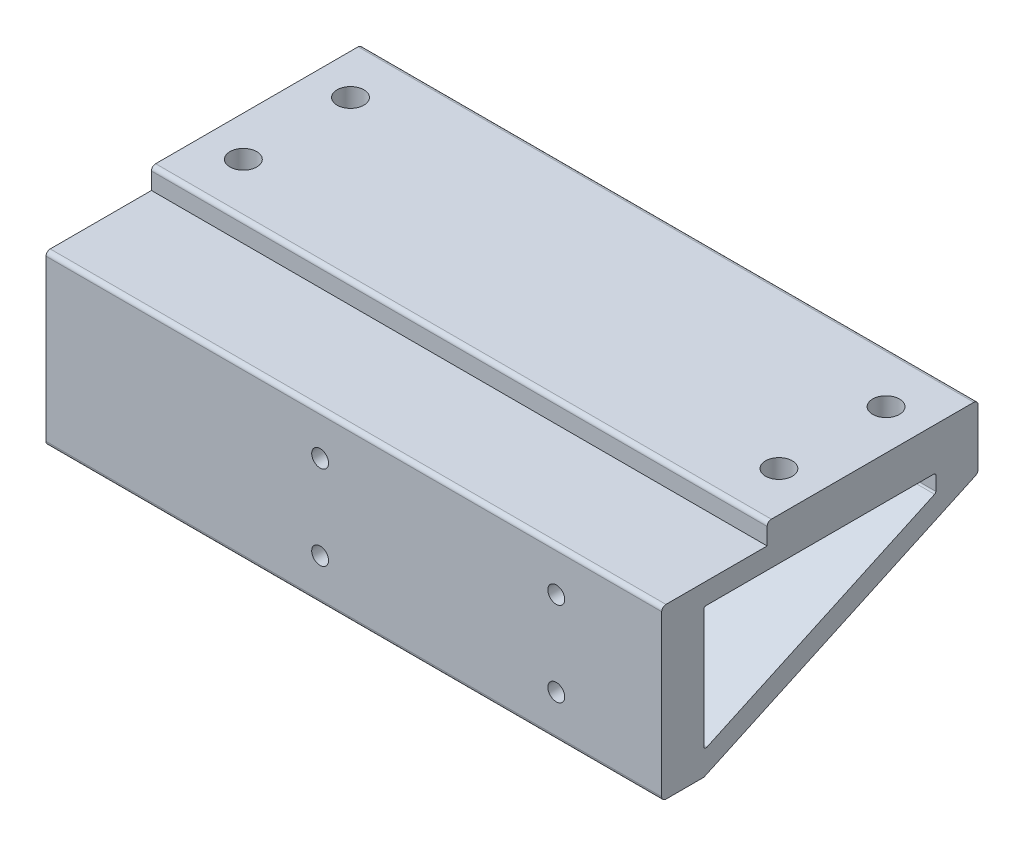
SolidWorks part; units mm, degrees
ref_plane "Front Plane" through (0, 0, 0) normal (0, 0, 1) x (1, 0, 0)
ref_plane "Top Plane" through (0, 0, 0) normal (0, 1, 0) x (1, 0, 0)
ref_plane "Right Plane" through (0, 0, 0) normal (1, 0, 0) x (0, 0, -1)
sketch "Sketch1" plane through (0, 0, 0) normal (0, 1, 0) x (1, 0, 0)
  line L1 (0, 0) -> (146, 0)
  line L2 (0, 0) -> (0, 50)
  line L3 (0, 50) -> (146, 50)
  line L4 (146, 0) -> (146, 50)
  dimension "D1" = 146
  dimension "D2" = 50
extrude "Boss-Extrude1" add sketch "Sketch1" along normal blind 5
ref_plane "Plane2" through (73, 0, 0) normal (-1, 0, 0) x (0, 0, 1)
sketch "Sketch9" plane through (0, 0, 0) normal (0, -1, 0) x (1, 0, 0)
  line L0 (146, 0) -> (146, -50) construction
  line L1 (146, -25) -> (135.6557, -25)
  line L2 (146, -25) -> (146, 21.4398)
  line L3 (146, 21.4398) -> (135.6557, 21.4398)
  line L4 (135.6557, -25) -> (135.6557, 21.4398)
sketch "Sketch10" plane through (146, 0, 0) normal (1, 0, 0) x (0, 0, -1)
  line L0 (-25, 0) -> (-25, -40)
  line L1 (-25, -40) -> (-15, -40)
  line L2 (50, 0) -> (50, -10)
  line L3 (-15, -40) -> (50, -10)
  line L4 (-15, -34.4931) -> (-15, -5)
  line L5 (-15, -5) -> (48.9018, -5) construction
  line L6 (48.9018, -5) -> (-15, -34.4931) construction
  line L7 (0, 0) -> (50, 0) construction
  line L8 (40, -5) -> (40, -9.1085)
  line L9 (-15, -5) -> (40, -5)
  line L10 (-15, -34.4931) -> (40, -9.1085)
  line L11 (-25, 0) -> (50, 0)
  line M8 (0, 0) -> (50, 0)
  dimension "D1" = 40
  dimension "D2" = 10
  dimension "D3" = 10
  dimension "D4" = 5
  dimension "D5" = 5
  dimension "D6" = 10
  dimension "D7" = 75
extrude "Boss-Extrude2" add sketch "Sketch10" against normal up to surface (146 mm away) contours L1 L3 L2 L0 L10 L4 L9 L8 M8 up to face at (0, 2.5, -25)
sketch "Sketch4" plane through (0, 5, 0) normal (0, 1, 0) x (1, 0, 0)
  line L0 (0, 25) -> (146, 25) construction
  line L1 (0, 50) -> (0, 0) construction
  line L2 (146, 0) -> (146, 50) construction
  line L3 (73, 50) -> (73, 0) construction
  line L4 (146, 50) -> (0, 50) construction
  line L5 (0, 0) -> (146, 0) construction
  line L6 (9.5, 37.7) -> (9.5, 12.3) construction
  line L7 (136.5, 25) -> (9.5, 25) construction
  circle A0 centre (9.5, 37.7) radius 3.175
  circle A1 centre (9.5, 12.3) radius 3.175
  circle A2 centre (136.5, 12.3) radius 3.175
  circle A3 centre (136.5, 37.7) radius 3.175
  point P15 (9.5, 25)
  point P18 (73, 25)
  dimension "D3" = 6.35
  dimension "D4" = 6.35
  dimension "D1" = 25.4
  dimension "D2" = 127
extrude "Cut-Extrude1" cut sketch "Sketch4" against normal blind 25
sketch "Sketch11" plane through (0, 0, 25) normal (0, 0, 1) x (1, 0, 0)
  line L0 (146, 0) -> (146, -40) construction
  line L1 (0, -40) -> (146, -40) construction
  circle A0 centre (121, -30) radius 2
  circle A1 centre (65, -30) radius 2
  circle A2 centre (65, -10) radius 2
  circle A3 centre (121, -10) radius 2
  dimension "D3" = 4
  dimension "D5" = 4
  dimension "D1" = 25
  dimension "D2" = 10
  dimension "D4" = 56
  dimension "D6" = 2
extrude "Cut-Extrude3" cut sketch "Sketch11" against normal blind 10
sketch "Sketch12" plane through (0, 0, 25) normal (0, 0, 1) x (1, 0, 0)
  line L0 (73, 5) -> (73, -40) construction
  line L1 (0, 5) -> (146, 5) construction
  line L2 (0, -40) -> (146, -40) construction
  line L3 (0, 0) -> (146, 0) construction
  line L4 (10, 0) -> (136, 0)
  line L5 (10, 0) -> (10, -10)
  line L6 (10, -10) -> (136, -10)
  line L7 (136, -10) -> (136, 0)
  point P6 (73, 0)
  point P12 (73, 0)
  dimension "D1" = 126
  dimension "D2" = 10
extrude "Cut-Extrude4" [suppressed] cut sketch "Sketch12" against normal blind 10
sketch "Sketch13" plane through (0, -40, 0) normal (0, -1, 0) x (1, 0, 0)
  line L0 (0, -50) -> (146, -50) construction
  line L1 (20, 15) -> (126, 15)
  line L2 (20, 15) -> (20, -50)
  line L3 (20, -50) -> (126, -50)
  line L4 (126, 15) -> (126, -50)
  line L5 (0, -50) -> (0, 15) construction
  line L7 (146, 15) -> (146, -50) construction
  line L8 (0, 15) -> (146, 15) construction
  dimension "D1" = 20
  dimension "D2" = 20
extrude "Cut-Extrude5" cut sketch "Sketch13" against normal up to surface (35 mm away) up to face at (73, -5, -24.8813)
fillet "Fillet1" radius 0.5 11 edges at (73, -5, 15) (10, -34.4931, 15) (136, -34.4931, 15) (15.8444, -9.1085, -40) (15.8444, -5, -40) (130.1556, -9.1085, -40) (130.1556, -5, -40) (142.3444, -5, -40) (142.3444, -9.1085, -40) (3.6556, -5, -40) (3.6556, -9.1085, -40)
fillet "Fillet2" radius 1 6 edges at (73, -40, 25) (10, -10, -50) (136, -10, -50) (73, 5, -50) (73, 5, 0) (73, 0, 25)
